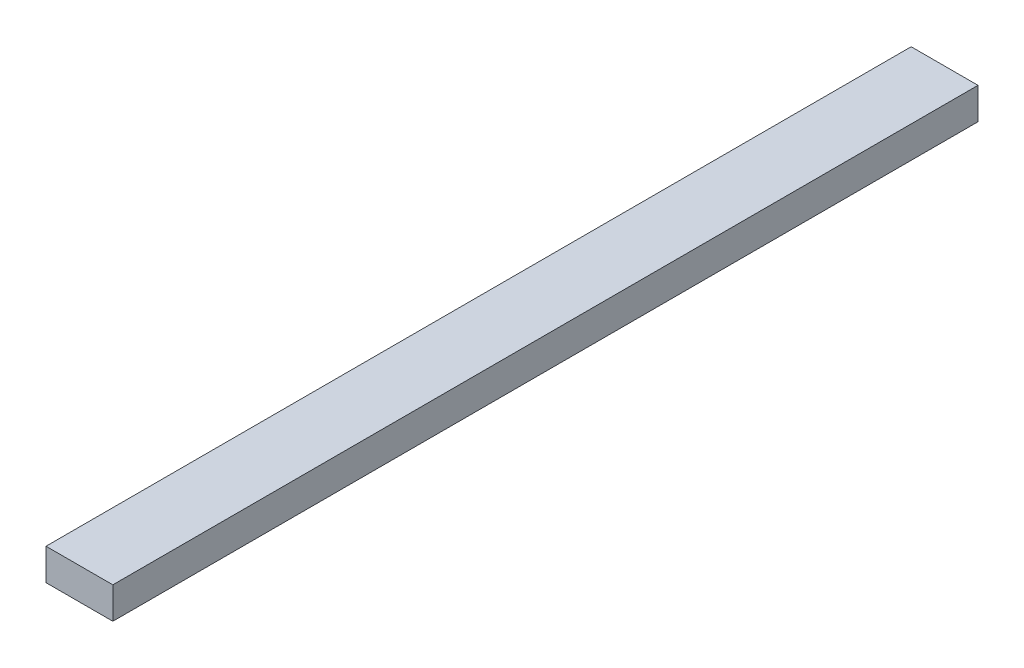
SolidWorks part; units mm, degrees
ref_plane "Front" through (0, 0, 0) normal (0, 0, 1) x (1, 0, 0)
ref_plane "Top" through (0, 0, 0) normal (0, 1, 0) x (1, 0, 0)
ref_plane "Right" through (0, 0, 0) normal (1, 0, 0) x (0, 0, -1)
sketch "Sketch1" plane through (0, 0, 0) normal (0, 0, 1) x (1, 0, 0)
  line L1 (3.175, -1.5) -> (-3.175, -1.5)
  line L2 (3.175, -1.5) -> (3.175, 1.5)
  line L3 (3.175, 1.5) -> (-3.175, 1.5)
  line L4 (-3.175, -1.5) -> (-3.175, 1.5)
  line L5 (3.175, -1.5) -> (-3.175, 1.5) construction
  line L6 (3.175, 1.5) -> (-3.175, -1.5) construction
  point P0 (0, 0)
  dimension "D1" = 6.35
  dimension "D2" = 3
extrude "Boss-Extrude1" add sketch "Sketch1" along normal blind 82.2
